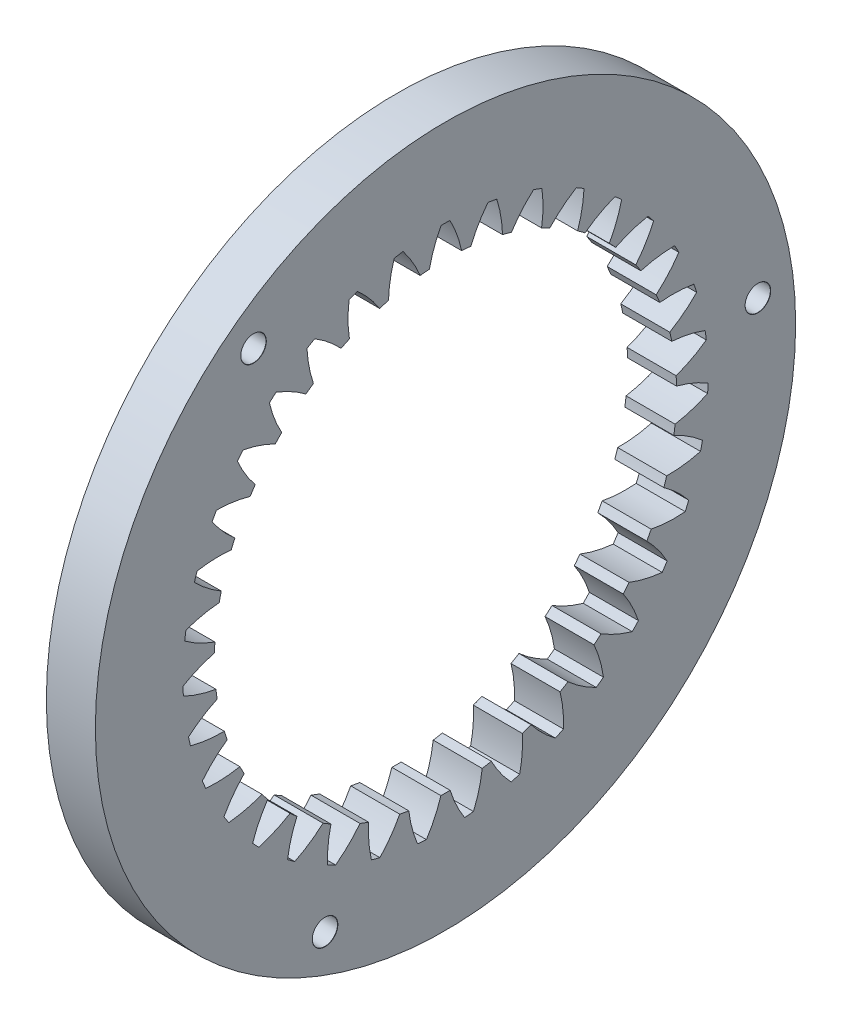
SolidWorks part; units mm, degrees
ref_plane "Front Plane" through (0, 0, 0) normal (0, 0, 1) x (1, 0, 0)
ref_plane "Top Plane" through (0, 0, 0) normal (0, 1, 0) x (1, 0, 0)
ref_plane "Right Plane" through (0, 0, 0) normal (1, 0, 0) x (0, 0, -1)
ref_plane "Plane1" through (-42.5819, 0, 0) normal (1, 0, 0) x (0, 0, -1)
sketch "Sketch1" plane through (-42.5819, 0, 0) normal (1, 0, 0) x (0, 0, -1)
  circle A0 centre (-27.7771, -7.0351) radius 50
  arc A1 (-24.1627, 25.7664) -> (-21.7087, 29.9717) centre (-7.9679, 19.1347) cw
  arc A2 (-21.7087, 29.9717) -> (-20.4553, 29.7442) centre (-27.7771, -7.0351) cw
  arc A3 (-20.4553, 29.7442) -> (-19.6354, 24.9448) centre (-37.1277, 24.4264) cw
  arc A4 (-19.6354, 24.9448) -> (-18.3638, 24.5939) centre (-27.7771, -7.0351) cw
  arc A5 (-18.3638, 24.5939) -> (-15.1984, 28.2934) centre (-3.6135, 15.1771) cw
  arc A6 (-15.1984, 28.2934) -> (-14.0057, 27.8458) centre (-27.7771, -7.0351) cw
  arc A7 (-14.0057, 27.8458) -> (-14.056, 22.9771) centre (-31.3598, 25.5905) cw
  arc A8 (-14.056, 22.9771) -> (-12.8675, 22.4048) centre (-27.7771, -7.0351) cw
  arc A9 (-12.8675, 22.4048) -> (-9.0924, 25.4797) centre (-0.0357, 10.5055) cw
  arc A10 (-9.0924, 25.4797) -> (-7.9988, 24.8263) centre (-27.7771, -7.0351) cw
  arc A11 (-7.9988, 24.8263) -> (-8.9176, 20.0448) centre (-25.4767, 25.7059) cw
  arc A12 (-8.9176, 20.0448) -> (-7.8505, 19.2695) centre (-27.7771, -7.0351) cw
  arc A13 (-7.8505, 19.2695) -> (-3.587, 21.6209) centre (2.6505, 5.2702) cw
  arc A14 (-3.587, 21.6209) -> (-2.6276, 20.7827) centre (-27.7771, -7.0351) cw
  arc A15 (-2.6276, 20.7827) -> (-4.3854, 16.2422) centre (-19.6676, 24.769) cw
  arc A16 (-4.3854, 16.2422) -> (-3.4738, 15.2887) centre (-27.7771, -7.0351) cw
  arc A17 (-3.4738, 15.2887) -> (1.141, 16.8411) centre (4.3587, -0.3606) cw
  arc A18 (1.141, 16.8411) -> (1.9353, 15.8451) centre (-27.7771, -7.0351) cw
  arc A19 (1.9353, 15.8451) -> (-0.605, 11.6914) centre (-14.1191, 22.8098) cw
  arc A20 (-0.605, 11.6914) -> (0.1217, 10.5905) centre (-27.7771, -7.0351) cw
  arc A21 (0.1217, 10.5905) -> (4.9395, 11.2938) centre (5.0341, -6.2059) cw
  arc A22 (4.9395, 11.2938) -> (5.5432, 10.172) centre (-27.7771, -7.0351) cw
  arc A23 (5.5432, 10.172) -> (2.3021, 6.5387) centre (-9.0095, 19.8915) cw
  arc A24 (2.3021, 6.5387) -> (2.8205, 5.3257) centre (-27.7771, -7.0351) cw
  arc A25 (2.8205, 5.3257) -> (7.6865, 5.1575) centre (4.6548, -12.0779) cw
  arc A26 (7.6865, 5.1575) -> (8.0802, 3.9459) centre (-27.7771, -7.0351) cw
  arc A27 (8.0802, 3.9459) -> (4.2423, 0.9497) centre (-4.5032, 16.1077) cw
  arc A28 (4.2423, 0.9497) -> (4.5359, -0.3363) centre (-27.7771, -7.0351) cw
  arc A29 (4.5359, -0.3363) -> (9.2937, -1.3707) centre (3.2332, -17.7878) cw
  arc A30 (9.2937, -1.3707) -> (9.4647, -2.6331) centre (-27.7771, -7.0351) cw
  arc A31 (9.4647, -2.6331) -> (5.1535, -4.8959) centre (-0.7449, 11.5801) cw
  arc A32 (5.1535, -4.8959) -> (5.2127, -6.2137) centre (-27.7771, -7.0351) cw
  arc A33 (5.2127, -6.2137) -> (9.7093, -8.081) centre (0.8149, -23.1521) cw
  arc A34 (9.7093, -8.081) -> (9.6522, -9.3536) centre (-27.7771, -7.0351) cw
  arc A35 (9.6522, -9.3536) -> (5.0063, -10.8103) centre (2.1445, 6.4541) cw
  arc A36 (5.0063, -10.8103) -> (4.8292, -12.1174) centre (-27.7771, -7.0351) cw
  arc A37 (4.8292, -12.1174) -> (8.9202, -14.7576) centre (-2.5224, -27.9984) cw
  arc A38 (8.9202, -14.7576) -> (8.6367, -15.9996) centre (-27.7771, -7.0351) cw
  arc A39 (8.6367, -15.9996) -> (3.8053, -16.6033) centre (4.0722, 0.8947) cw
  arc A40 (3.8053, -16.6033) -> (3.3977, -17.8578) centre (-27.7771, -7.0351) cw
  arc A41 (3.3977, -17.8578) -> (6.9515, -21.1861) centre (-6.6714, -32.1709) cw
  arc A42 (6.9515, -21.1861) -> (6.4508, -22.3575) centre (-27.7771, -7.0351) cw
  arc A43 (6.4508, -22.3575) -> (1.5893, -22.0888) centre (4.9763, -4.9197) cw
  arc A44 (1.5893, -22.0888) -> (0.9642, -23.2504) centre (-27.7771, -7.0351) cw
  arc A45 (0.9642, -23.2504) -> (3.8666, -27.1597) centre (-11.4988, -35.5355) cw
  arc A46 (3.8666, -27.1597) -> (3.1648, -28.2229) centre (-27.7771, -7.0351) cw
  arc A47 (3.1648, -28.2229) -> (-1.5706, -27.0904) centre (4.8277, -10.802) cw
  arc A48 (-1.5706, -27.0904) -> (-2.393, -28.1218) centre (-27.7771, -7.0351) cw
  arc A49 (-2.393, -28.1218) -> (-0.2353, -32.4865) centre (-16.8493, -37.9841) cw
  arc A50 (-0.2353, -32.4865) -> (-1.1156, -33.4072) centre (-27.7771, -7.0351) cw
  arc A51 (-1.1156, -33.4072) -> (-5.5728, -31.4475) centre (3.6311, -16.5633) cw
  arc A52 (-5.5728, -31.4475) -> (-6.5661, -32.3154) centre (-27.7771, -7.0351) cw
  arc A53 (-6.5661, -32.3154) -> (-5.2224, -36.9952) centre (-22.5511, -39.438) cw
  arc A54 (-5.2224, -36.9952) -> (-6.253, -37.744) centre (-27.7771, -7.0351) cw
  arc A55 (-6.253, -37.744) -> (-10.2886, -35.0199) centre (1.425, -22.0183) cw
  arc A56 (-10.2886, -35.0199) -> (-11.421, -35.6965) centre (-27.7771, -7.0351) cw
  arc A57 (-11.421, -35.6965) -> (-10.9345, -40.541) centre (-28.4208, -39.8504) cw
  arc A58 (-10.9345, -40.541) -> (-12.0822, -41.0938) centre (-27.7771, -7.0351) cw
  arc A59 (-12.0822, -41.0938) -> (-15.5665, -37.6929) centre (-1.7197, -26.9918) cw
  arc A60 (-15.5665, -37.6929) -> (-16.8015, -38.1564) centre (-27.7771, -7.0351) cw
  arc A61 (-16.8015, -38.1564) -> (-17.1879, -43.01) centre (-34.2699, -39.2081) cw
  arc A62 (-17.1879, -43.01) -> (-18.4159, -43.3489) centre (-27.7771, -7.0351) cw
  arc A63 (-18.4159, -43.3489) -> (-21.2369, -39.3805) centre (-5.7018, -31.3238) cw
  arc A64 (-21.2369, -39.3805) -> (-22.5348, -39.616) centre (-27.7771, -7.0351) cw
  arc A65 (-22.5348, -39.616) -> (-23.7816, -44.3226) centre (-39.9103, -37.5317) cw
  arc A66 (-23.7816, -44.3226) -> (-25.0504, -44.4368) centre (-27.7771, -7.0351) cw
  arc A67 (-25.0504, -44.4368) -> (-27.1175, -40.0285) centre (-10.3935, -34.8751) cw
  arc A68 (-27.1175, -40.0285) -> (-28.4366, -40.0285) centre (-27.7771, -7.0351) cw
  arc A69 (-28.4366, -40.0285) -> (-30.5038, -44.4368) centre (-45.1607, -34.8751) cw
  arc A70 (-30.5038, -44.4368) -> (-31.7726, -44.3226) centre (-27.7771, -7.0351) cw
  arc A71 (-31.7726, -44.3226) -> (-33.0193, -39.616) centre (-15.6439, -37.5317) cw
  arc A72 (-33.0193, -39.616) -> (-34.3172, -39.3805) centre (-27.7771, -7.0351) cw
  arc A73 (-34.3172, -39.3805) -> (-37.1383, -43.3489) centre (-49.8523, -31.3238) cw
  arc A74 (-37.1383, -43.3489) -> (-38.3663, -43.01) centre (-27.7771, -7.0351) cw
  arc A75 (-38.3663, -43.01) -> (-38.7526, -38.1564) centre (-21.2843, -39.2081) cw
  arc A76 (-38.7526, -38.1564) -> (-39.9876, -37.6929) centre (-27.7771, -7.0351) cw
  arc A77 (-39.9876, -37.6929) -> (-43.4719, -41.0938) centre (-53.8345, -26.9918) cw
  arc A78 (-43.4719, -41.0938) -> (-44.6197, -40.541) centre (-27.7771, -7.0351) cw
  arc A79 (-44.6197, -40.541) -> (-44.1332, -35.6965) centre (-27.1333, -39.8504) cw
  arc A80 (-44.1332, -35.6965) -> (-45.2656, -35.0199) centre (-27.7771, -7.0351) cw
  arc A81 (-45.2656, -35.0199) -> (-49.3011, -37.744) centre (-56.9792, -22.0183) cw
  arc A82 (-49.3011, -37.744) -> (-50.3318, -36.9952) centre (-27.7771, -7.0351) cw
  arc A83 (-50.3318, -36.9952) -> (-48.988, -32.3154) centre (-33.0031, -39.438) cw
  arc A84 (-48.988, -32.3154) -> (-49.9814, -31.4475) centre (-27.7771, -7.0351) cw
  arc A85 (-49.9814, -31.4475) -> (-54.4385, -33.4072) centre (-59.1852, -16.5633) cw
  arc A86 (-54.4385, -33.4072) -> (-55.3189, -32.4865) centre (-27.7771, -7.0351) cw
  arc A87 (-55.3189, -32.4865) -> (-53.1611, -28.1218) centre (-38.7049, -37.9841) cw
  arc A88 (-53.1611, -28.1218) -> (-53.9836, -27.0904) centre (-27.7771, -7.0351) cw
  arc A89 (-53.9836, -27.0904) -> (-58.719, -28.2229) centre (-60.3818, -10.802) cw
  arc A90 (-58.719, -28.2229) -> (-59.4208, -27.1597) centre (-27.7771, -7.0351) cw
  arc A91 (-59.4208, -27.1597) -> (-56.5184, -23.2504) centre (-44.0554, -35.5355) cw
  arc A92 (-56.5184, -23.2504) -> (-57.1435, -22.0888) centre (-27.7771, -7.0351) cw
  arc A93 (-57.1435, -22.0888) -> (-62.005, -22.3575) centre (-60.5305, -4.9197) cw
  arc A94 (-62.005, -22.3575) -> (-62.5057, -21.1861) centre (-27.7771, -7.0351) cw
  arc A95 (-62.5057, -21.1861) -> (-58.9519, -17.8578) centre (-48.8828, -32.1709) cw
  arc A96 (-58.9519, -17.8578) -> (-59.3595, -16.6033) centre (-27.7771, -7.0351) cw
  arc A97 (-59.3595, -16.6033) -> (-64.1908, -15.9996) centre (-59.6264, 0.8947) cw
  arc A98 (-64.1908, -15.9996) -> (-64.4743, -14.7576) centre (-27.7771, -7.0351) cw
  arc A99 (-64.4743, -14.7576) -> (-60.3834, -12.1174) centre (-53.0318, -27.9984) cw
  arc A100 (-60.3834, -12.1174) -> (-60.5604, -10.8103) centre (-27.7771, -7.0351) cw
  arc A101 (-60.5604, -10.8103) -> (-65.2063, -9.3536) centre (-57.6987, 6.4541) cw
  arc A102 (-65.2063, -9.3536) -> (-65.2635, -8.081) centre (-27.7771, -7.0351) cw
  arc A103 (-65.2635, -8.081) -> (-60.7669, -6.2137) centre (-56.3691, -23.1521) cw
  arc A104 (-60.7669, -6.2137) -> (-60.7077, -4.8959) centre (-27.7771, -7.0351) cw
  arc A105 (-60.7077, -4.8959) -> (-65.0188, -2.6331) centre (-54.8092, 11.5801) cw
  arc A106 (-65.0188, -2.6331) -> (-64.8478, -1.3707) centre (-27.7771, -7.0351) cw
  arc A107 (-64.8478, -1.3707) -> (-60.09, -0.3363) centre (-58.7874, -17.7878) cw
  arc A108 (-60.09, -0.3363) -> (-59.7965, 0.9497) centre (-27.7771, -7.0351) cw
  arc A109 (-59.7965, 0.9497) -> (-63.6343, 3.9459) centre (-51.051, 16.1077) cw
  arc A110 (-63.6343, 3.9459) -> (-63.2407, 5.1575) centre (-27.7771, -7.0351) cw
  arc A111 (-63.2407, 5.1575) -> (-58.3747, 5.3257) centre (-60.209, -12.0779) cw
  arc A112 (-58.3747, 5.3257) -> (-57.8562, 6.5387) centre (-27.7771, -7.0351) cw
  arc A113 (-57.8562, 6.5387) -> (-61.0974, 10.172) centre (-46.5446, 19.8915) cw
  arc A114 (-61.0974, 10.172) -> (-60.4937, 11.2938) centre (-27.7771, -7.0351) cw
  arc A115 (-60.4937, 11.2938) -> (-55.6758, 10.5905) centre (-60.5882, -6.2059) cw
  arc A116 (-55.6758, 10.5905) -> (-54.9492, 11.6914) centre (-27.7771, -7.0351) cw
  arc A117 (-54.9492, 11.6914) -> (-57.4895, 15.8451) centre (-41.4351, 22.8098) cw
  arc A118 (-57.4895, 15.8451) -> (-56.6952, 16.8411) centre (-27.7771, -7.0351) cw
  arc A119 (-56.6952, 16.8411) -> (-52.0803, 15.2887) centre (-59.9129, -0.3606) cw
  arc A120 (-52.0803, 15.2887) -> (-51.1688, 16.2422) centre (-27.7771, -7.0351) cw
  arc A121 (-51.1688, 16.2422) -> (-52.9266, 20.7827) centre (-35.8866, 24.769) cw
  arc A122 (-52.9266, 20.7827) -> (-51.9672, 21.6209) centre (-27.7771, -7.0351) cw
  arc A123 (-51.9672, 21.6209) -> (-47.7037, 19.2695) centre (-58.2047, 5.2702) cw
  arc A124 (-47.7037, 19.2695) -> (-46.6365, 20.0448) centre (-27.7771, -7.0351) cw
  arc A125 (-46.6365, 20.0448) -> (-47.5553, 24.8263) centre (-30.0775, 25.7059) cw
  arc A126 (-47.5553, 24.8263) -> (-46.4617, 25.4797) centre (-27.7771, -7.0351) cw
  arc A127 (-46.4617, 25.4797) -> (-42.6866, 22.4048) centre (-55.5185, 10.5055) cw
  arc A128 (-42.6866, 22.4048) -> (-41.4982, 22.9771) centre (-27.7771, -7.0351) cw
  arc A129 (-41.4982, 22.9771) -> (-41.5484, 27.8458) centre (-24.1944, 25.5905) cw
  arc A130 (-41.5484, 27.8458) -> (-40.3557, 28.2934) centre (-27.7771, -7.0351) cw
  arc A131 (-40.3557, 28.2934) -> (-37.1903, 24.5939) centre (-51.9407, 15.1771) cw
  arc A132 (-37.1903, 24.5939) -> (-35.9188, 24.9448) centre (-27.7771, -7.0351) cw
  arc A133 (-35.9188, 24.9448) -> (-35.0989, 29.7442) centre (-18.4264, 24.4264) cw
  arc A134 (-35.0989, 29.7442) -> (-33.8455, 29.9717) centre (-27.7771, -7.0351) cw
  arc A135 (-33.8455, 29.9717) -> (-31.3915, 25.7664) centre (-47.5863, 19.1347) cw
  arc A136 (-31.3915, 25.7664) -> (-30.0777, 25.8847) centre (-27.7771, -7.0351) cw
  arc A137 (-30.0777, 25.8847) -> (-28.414, 30.4605) centre (-12.959, 22.2512) cw
  arc A138 (-28.414, 30.4605) -> (-27.1401, 30.4605) centre (-27.7771, -7.0351) cw
  arc A139 (-27.1401, 30.4605) -> (-25.4765, 25.8847) centre (-42.5951, 22.2512) cw
  arc A140 (-25.4765, 25.8847) -> (-24.1627, 25.7664) centre (-27.7771, -7.0351) cw
extrude "Boss-Extrude1" add sketch "Sketch1" against normal blind 7
hole_wizard "CSK for M3 Countersunk Flat Head Screw1" positions "Sketch2" profile "Sketch3" countersink size "M3" standard "ISO" end condition up to next
sketch "Sketch2" plane through (-49.5819, 0, 0) normal (-1, 0, 0) x (0, 0, 1)
  line L2 (44.9758, -48.6188) -> (-16.8348, -1.1377) construction
  line L3 (-16.8348, -1.1377) -> (55.1903, 28.6513) construction
  line L4 (55.1903, 28.6513) -> (44.9758, -48.6188) construction
  circle A0 centre (27.7771, -7.0351) radius 45 construction
  circle A1 centre (27.7771, -7.0351) radius 50 construction
  point P0 (-16.8348, -1.1377)
  point P2 (55.1903, 28.6513)
  point P4 (44.9758, -48.6188)
  point P22 (0, 0)
  point P23 (0, 0)
  point P26 (54.627, 27.9181)
  dimension "D1" = 90
sketch "Sketch3" plane through (-49.5819, -1.1377, -16.8348) normal (0, 1, 0) x (0, 0, 1)
  line L0 (0, 0) -> (0, 7)
  line L1 (0, 7) -> (1.825, 7)
  line L2 (1.8, 6.975) -> (1.8, 1.35)
  line L3 (1.8, 1.35) -> (3.15, 0)
  line L5 (3.15, 0) -> (0, 0)
  line L6 (-1.8, 1.35) -> (-3.15, 0) construction
  line L7 (1.825, 7) -> (1.8, 6.975)
  line L8 (-1.825, 7) -> (-1.8, 6.975) construction
  line L11 (0, -6.35) -> (0, 107.95) construction
  dimension "Thru Hole Dia." = 3.6
  dimension "Thru Hole Depth" = 7
  dimension "Near C'Sink Dia." = 6.3
  dimension "Near C'Sink Angle" = 90
  dimension "Far C'Sink Dia." = 3.65
  dimension "Far C'Sink Angle" = 90
